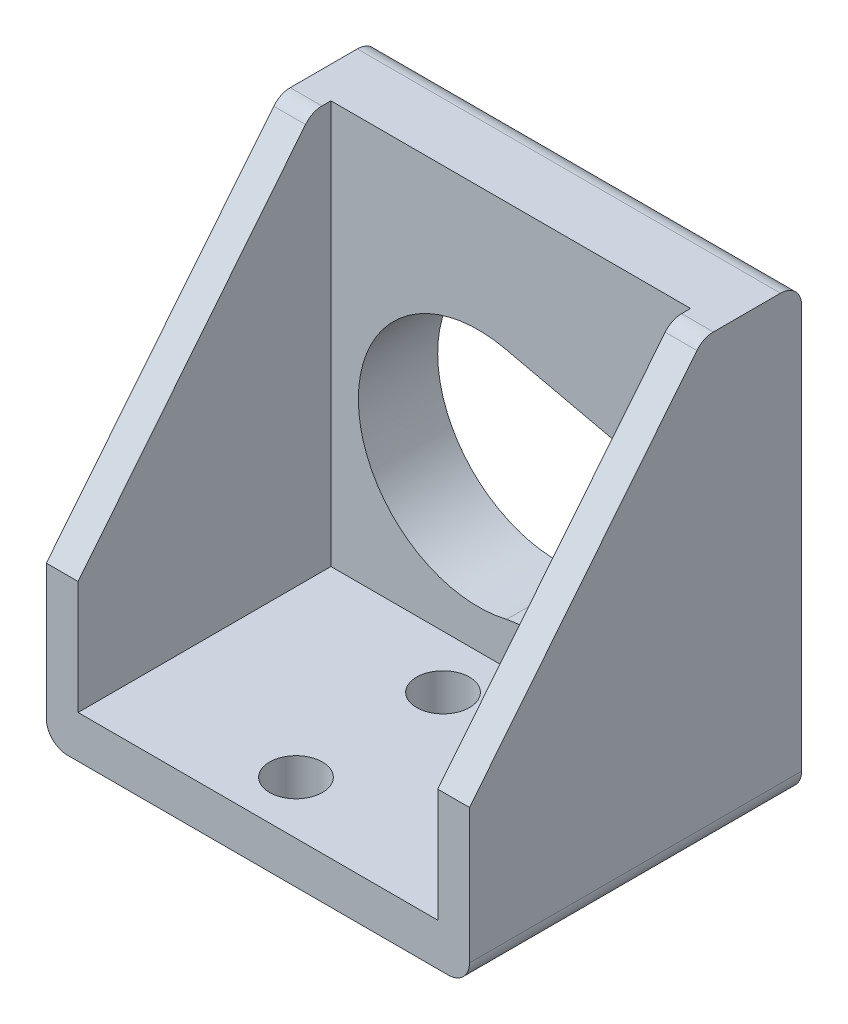
SolidWorks part; units mm, degrees
ref_plane "Front Plane" through (0, 0, 0) normal (0, 0, 1) x (1, 0, 0)
ref_plane "Top Plane" through (0, 0, 0) normal (0, 1, 0) x (1, 0, 0)
ref_plane "Right Plane" through (0, 0, 0) normal (1, 0, 0) x (0, 0, -1)
sketch "Sketch1" plane through (0, 0, 0) normal (0, 1, 0) x (1, 0, 0)
  line L1 (0, 0) -> (50.8, 0)
  line L2 (0, 0) -> (0, 39.878)
  line L3 (0, 39.878) -> (50.8, 39.878)
  line L4 (50.8, 0) -> (50.8, 39.878)
  dimension "D1" = 39.878
  dimension "D2" = 50.8
extrude "Boss-Extrude1" add sketch "Sketch1" along normal blind 53.4999
sketch "Sketch3" plane through (0, 0, 0) normal (0, 0, 1) x (1, 0, 0)
  line L0 (0, 0) -> (50.8, 0) construction
  line L1 (3.81, 5.08) -> (46.99, 5.08)
  line L2 (3.81, 5.08) -> (3.81, 55.88)
  line L3 (3.81, 55.88) -> (46.99, 55.88)
  line L4 (46.99, 5.08) -> (46.99, 55.88)
  line L5 (0, 53.4999) -> (0, 0) construction
  dimension "D1" = 5.08
  dimension "D2" = 3.81
  dimension "D3" = 50.8
  dimension "D4" = 43.18
extrude "Cut-Extrude1" cut sketch "Sketch3" against normal blind 30.353 contours L2 L3 L4 L1
sketch "Sketch4" plane through (0, 0, 0) normal (-1, 0, 0) x (0, 0, 1)
  line L0 (0, 18.7019) -> (-28.067, 53.4999)
  line L1 (0, 53.4999) -> (0, 0) construction
  line L2 (-39.878, 53.4999) -> (0, 53.4999) construction
  line L3 (-28.067, 53.4999) -> (0, 53.4999)
  line L4 (0, 53.4999) -> (0, 18.7019)
  dimension "D1" = 28.067
  dimension "D2" = 34.798
extrude "Cut-Extrude2" cut sketch "Sketch4" against normal through all
fillet "Fillet3" radius 2.54 1 edges at (25.4, 53.4999, -39.878)
fillet "Fillet4" radius 2.54 2 edges at (1.905, 53.4999, -28.067) (48.895, 53.4999, -28.067)
fillet "Fillet5" radius 2.54 2 edges at (50.8, 0, -19.939) (0, 0, -19.939)
sketch "Sketch5" plane through (0, 5.08, 0) normal (0, 1, 0) x (1, 0, 0)
  line L0 (0, 27.3045) -> (0, 0) construction
  line L1 (3.81, 0) -> (46.99, 0) construction
  circle A0 centre (23.622, 6.35) radius 3.175
  circle A1 centre (23.622, 24.003) radius 3.175
  dimension "D3" = 6.35
  dimension "D4" = 17.653
  dimension "D6" = 6.35
  dimension "D1" = 23.622
  dimension "D2" = 6.35
  dimension "D5" = 23.622
extrude "Cut-Extrude3" cut sketch "Sketch5" against normal through all contours A0 | A1
ref_plane "Plane8" through (50.8, 2.54, -39.878) normal (0, -1, 0) x (-1, 0, 0)
sketch "Sketch13" plane through (0, 0, -30.353) normal (0, 0, 1) x (1, 0, 0)
  line L0 (45.0785, 33.5411) -> (45.0785, 13.162)
  line L1 (45.0785, 13.162) -> (24.902, 10.1329)
  line L2 (45.0785, 33.5411) -> (24.7122, 38.1818)
  arc A0 (24.7122, 38.1818) -> (24.902, 10.1329) centre (21.5114, 24.1351) ccw
  dimension "D1" = 23.567
  dimension "D2" = 14.4068
  dimension "D3" = 23.567
sketch "Sketch15" plane through (0, 0, -30.353) normal (0, 0, 1) x (1, 0, 0)
extrude "Cut-Extrude4" cut sketch "Sketch13" against normal blind 25.4
equation "\"1f\"=0.1"
